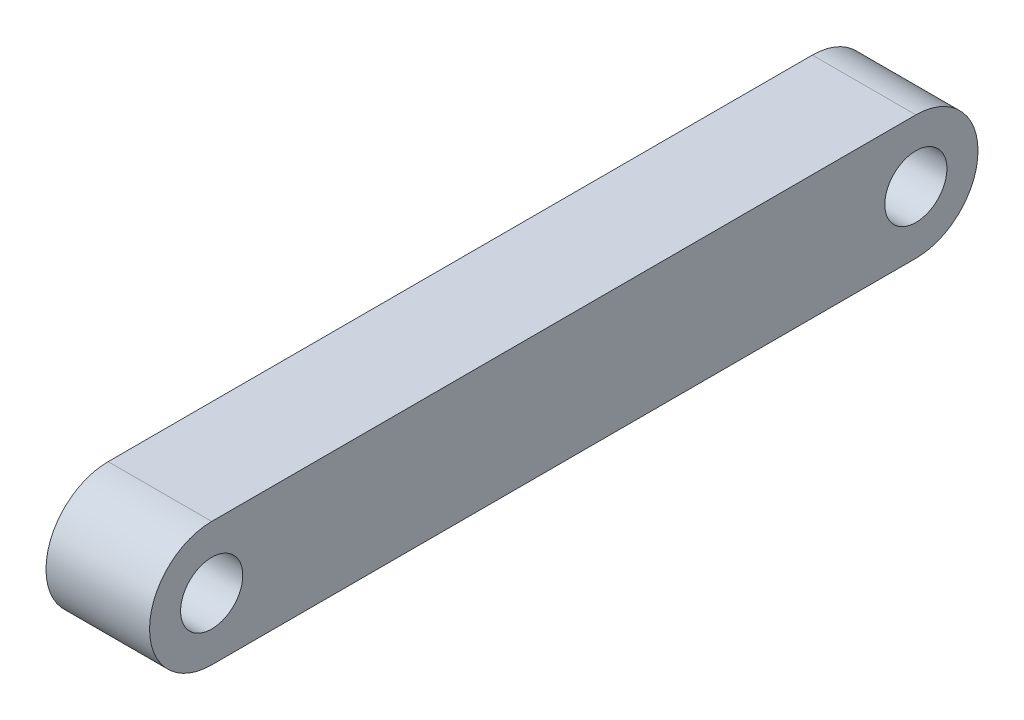
SolidWorks part; units mm, degrees
ref_plane "前视基准面" through (0, 0, 0) normal (0, 0, 1) x (1, 0, 0)
ref_plane "上视基准面" through (0, 0, 0) normal (0, 1, 0) x (1, 0, 0)
ref_plane "右视基准面" through (0, 0, 0) normal (1, 0, 0) x (0, 0, -1)
other "Configuration Table"
sketch "草图1" plane through (0, 0, 0) normal (1, 0, 0) x (0, 0, -1)
  line L0 (-17, 0) -> (17, 0) construction
  line L1 (-17, 0) -> (17, 0) construction
  line L2 (-17, 3) -> (17, 3)
  line L3 (-17, -3) -> (17, -3)
  circle A0 centre (17, 0) radius 1.5
  circle A1 centre (-17, 0) radius 1.5
  arc A2 (-17, 3) -> (-17, -3) centre (-17, 0) ccw
  arc A3 (17, -3) -> (17, 3) centre (17, 0) ccw
  point P4 (0, 0)
  point P8 (0, 0)
  dimension "D2" = 3
  dimension "D3" = 3
  dimension "D1" = 34
extrude "凸台-拉伸1" add sketch "草图1" along normal mid plane 5
